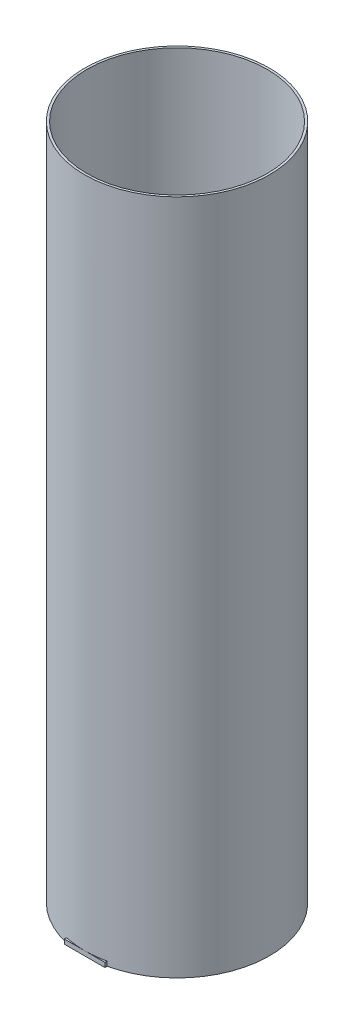
SolidWorks part; units mm, degrees
ref_plane "Front Plane" through (0, 0, 0) normal (0, 0, 1) x (1, 0, 0)
ref_plane "Top Plane" through (0, 0, 0) normal (0, 1, 0) x (1, 0, 0)
ref_plane "Right Plane" through (0, 0, 0) normal (1, 0, 0) x (0, 0, -1)
sketch "Sketch1" plane through (0, 0, 0) normal (0, 1, 0) x (1, 0, 0)
  circle A0 centre (0, 0) radius 50.8
  circle A1 centre (0, 0) radius 52.07
  dimension "D1" = 101.6
  dimension "D2" = 104.14
extrude "Boss-Extrude1" add sketch "Sketch1" along normal blind 381
sketch "Sketch2" plane through (0, 0, 0) normal (0, -1, 0) x (1, 0, 0)
  line L0 (0, 52.07) -> (-11.43, 52.07)
  line L1 (-11.43, 52.07) -> (-11.43, 50.8)
  line L2 (-11.43, 50.8) -> (11.43, 50.8)
  line L3 (11.43, 50.8) -> (11.43, 52.07)
  line L4 (11.43, 52.07) -> (0, 52.07)
  circle A0 centre (0, 0) radius 50.8 construction
  circle A1 centre (0, 0) radius 52.07
  circle A2 centre (0, 0) radius 52.07
  point P5 (0, 50.8)
  point P9 (0, 50.8)
  point P12 (0, 50.8)
  point P13 (0, 0)
  circle M5 centre (0, 0) radius 52.07
  dimension "D1" = 0
extrude "Boss-Extrude2" add sketch "Sketch2" against normal blind 2.54 contours L3 L4 M5 | L2 M5 | L0 L1 M5
